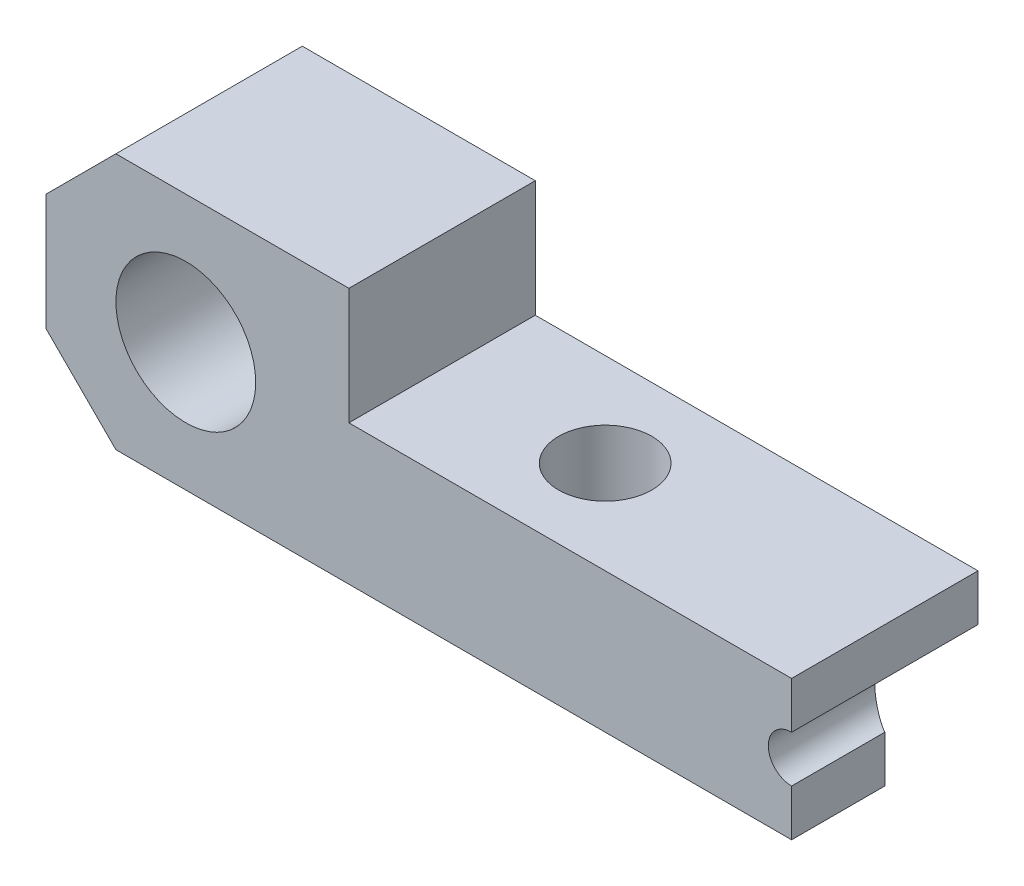
SolidWorks part; units mm, degrees
material "Alliage 7079"
ref_plane "Face" through (0, 0, 0) normal (0, 0, 1) x (1, 0, 0)
ref_plane "Dessus" through (0, 0, 0) normal (0, 1, 0) x (1, 0, 0)
ref_plane "Droite" through (0, 0, 0) normal (1, 0, 0) x (0, 0, -1)
sketch "Esquisse1" plane through (0, 0, 0) normal (0, 0, 1) x (1, 0, 0)
  line L0 (32, 6) -> (13, 6)
  line L1 (0, 0) -> (32, 0)
  line L2 (0, 0) -> (0, 11)
  line L3 (0, 11) -> (13, 11)
  line L4 (32, 0) -> (32, 6)
  line L6 (13, 11) -> (13, 6)
  circle A0 centre (6, 5.5) radius 3
  dimension "D5" = 6
  dimension "D1" = 19
  dimension "D2" = 11
  dimension "D3" = 5
  dimension "D4" = 13
  dimension "D6" = 6
  dimension "D7" = 5.5
extrude "Extrusion1" add sketch "Esquisse1" along normal blind 8
sketch "Esquisse2" plane through (0, 0, 8) normal (0, 0, 1) x (1, 0, 0)
  line L0 (33.0277, 3) -> (20.4257, 3) construction
  line L1 (32, 6) -> (13, 6) construction
  line L2 (0, 0) -> (32, 0) construction
  line L3 (32, 0) -> (32, 6) construction
  circle A0 centre (32, 3) radius 1
  dimension "D1" = 2
extrude "Enlèv. mat.-Extru.1" cut sketch "Esquisse2" against normal through all
sketch "Esquisse3" plane through (0, 0, 0) normal (0, -1, 0) x (1, 0, 0)
  line L1 (0, 0) -> (32, 0) construction
  line L2 (25, 0) -> (32, 4)
  line L3 (32, 8) -> (32, 0) construction
  line L4 (32, 4) -> (32, 0)
  line L5 (32, 0) -> (25, 0)
  line L6 (0, 8) -> (0, 0) construction
  dimension "D1" = 25
  dimension "D2" = 4
extrude "Enlèv. mat.-Extru.4" cut sketch "Esquisse3" against normal blind 4
sketch "Esquisse4" plane through (0, 0, 0) normal (0, -1, 0) x (1, 0, 0)
  line L0 (32, 8) -> (32, 4) construction
  line L1 (0, 8) -> (32, 8) construction
  circle A0 centre (20, 4) radius 2
  dimension "D1" = 4
  dimension "D2" = 12
  dimension "D3" = 4
extrude "Enlèv. mat.-Extru.5" cut sketch "Esquisse4" against normal through all
chamfer "Chanfrein1" distance 3 angle 45 2 edges at (0, 0, 4) (0, 11, 4)
